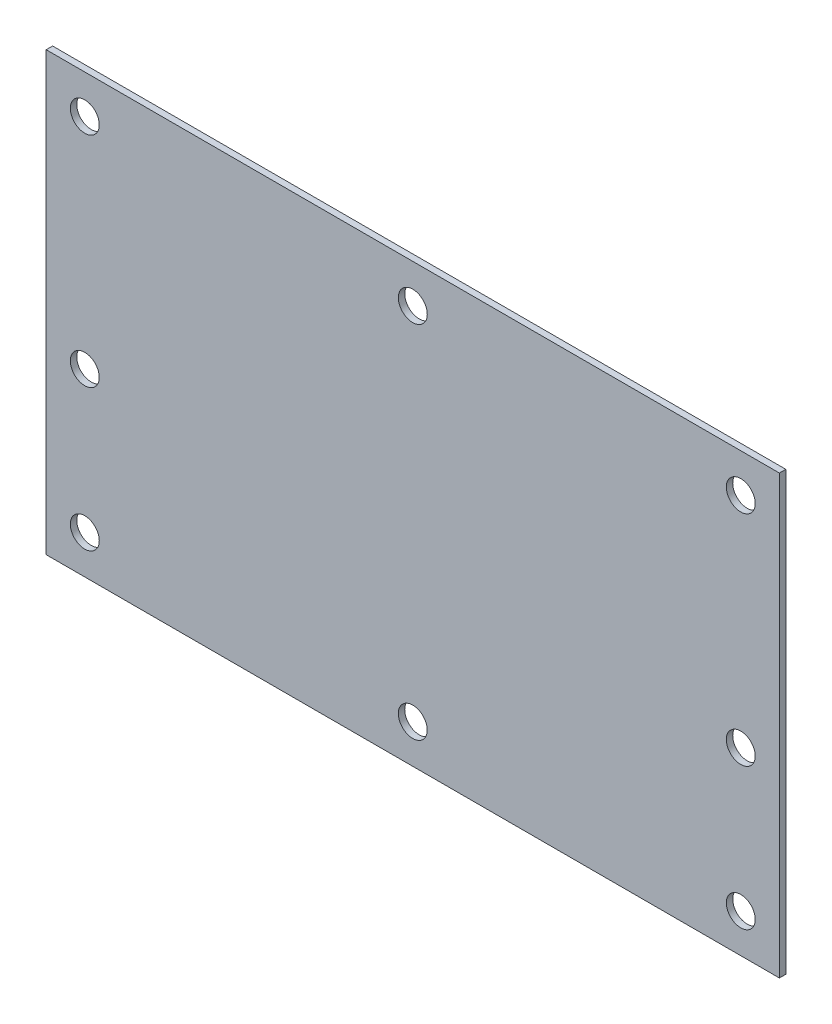
SolidWorks part; units mm, degrees
ref_plane "Спереди" through (0, 0, 0) normal (0, 0, 1) x (1, 0, 0)
ref_plane "Сверху" through (0, 0, 0) normal (0, 1, 0) x (1, 0, 0)
ref_plane "Справа" through (0, 0, 0) normal (1, 0, 0) x (0, 0, -1)
sketch "Эскиз1" plane through (0, 0, 0) normal (0, 0, 1) x (1, 0, 0)
  line L1 (0, 0) -> (114, 0)
  line L2 (0, 0) -> (0, 68)
  line L3 (0, 68) -> (114, 68)
  line L4 (114, 0) -> (114, 68)
  dimension "D1" = 114
  dimension "D2" = 68
extrude "Бобышка-Вытянуть1" add sketch "Эскиз1" along normal blind 1
sketch "Эскиз2" plane through (0, 0, 1) normal (0, 0, 1) x (1, 0, 0)
  line L0 (6, 62) -> (6, 6) construction
  line L1 (6, 6) -> (108, 6) construction
  line L2 (108, 6) -> (108, 62) construction
  line L3 (108, 62) -> (6, 62) construction
  line L4 (6, 28) -> (108, 28) construction
  line L5 (0, 68) -> (0, 0) construction
  line L6 (57, 62) -> (57, 6) construction
  line L7 (114, 0) -> (114, 68) construction
  line L8 (0, 0) -> (114, 0) construction
  line L9 (114, 68) -> (0, 68) construction
  circle A0 centre (6, 62) radius 2.25
  circle A1 centre (6, 28) radius 2.25
  circle A2 centre (6, 6) radius 2.25
  circle A3 centre (57, 6) radius 2.25
  circle A4 centre (57, 62) radius 2.25
  circle A5 centre (108, 62) radius 2.25
  circle A6 centre (108, 28) radius 2.25
  circle A7 centre (108, 6) radius 2.25
  point P28 (0, 0)
  point P30 (59, 36.3689)
  point P32 (0, 0)
  point P34 (0, 0)
  point P35 (55, 31.4)
  dimension "D6" = 4.5
  dimension "D1" = 6
  dimension "D2" = 6
  dimension "D3" = 6
  dimension "D4" = 22
  dimension "D5" = 6
extrude "Вырез-Вытянуть1" cut sketch "Эскиз2" against normal up to next
